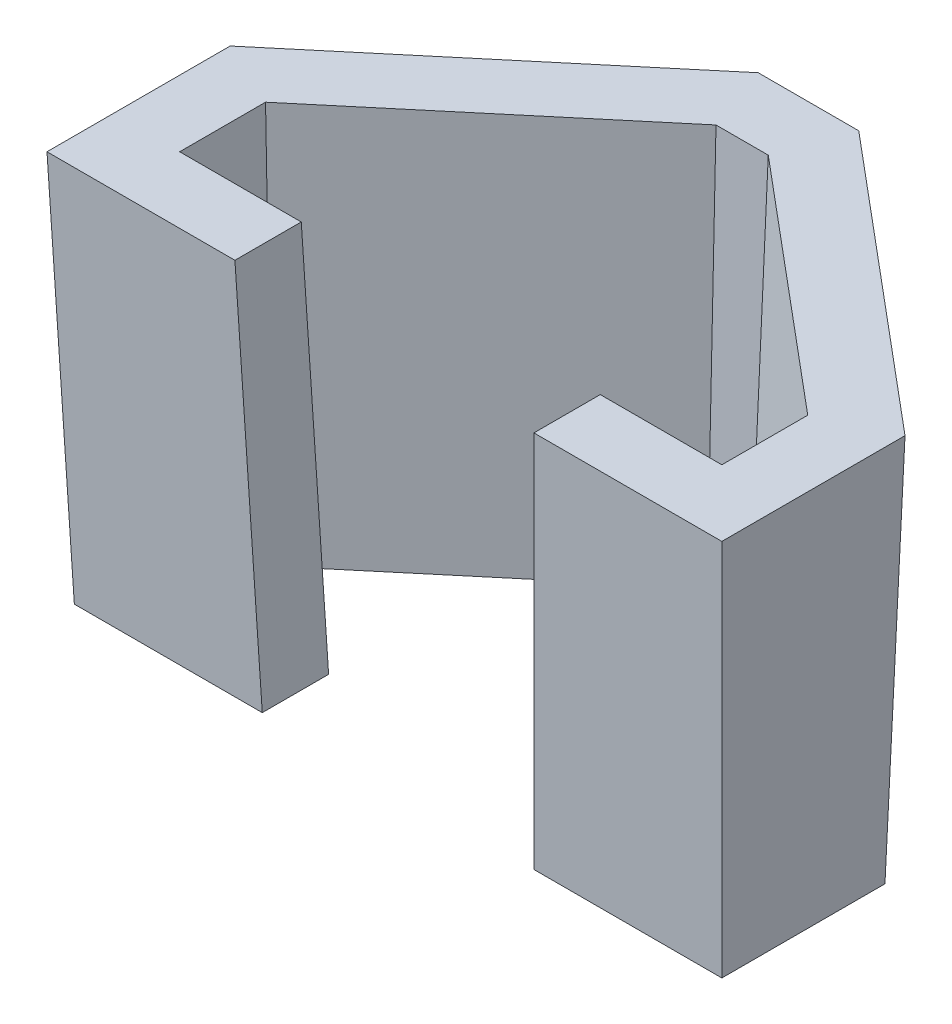
SolidWorks part; units mm, degrees
ref_plane "Alzado" through (0, 0, 0) normal (0, 0, 1) x (1, 0, 0)
ref_plane "Planta" through (0, 0, 0) normal (0, 1, 0) x (1, 0, 0)
ref_plane "Vista lateral" through (0, 0, 0) normal (1, 0, 0) x (0, 0, -1)
sketch "Croquis1" plane through (0, 0, 0) normal (0, 1, 0) x (1, 0, 0)
  line L0 (0, 0) -> (98.55, 0)
  line L1 (98.55, 0) -> (98.55, 12.6)
  line L2 (98.55, 12.6) -> (53.325, 50.5373)
  line L3 (53.325, 50.5373) -> (45.225, 50.5373)
  line L4 (45.225, 50.5373) -> (0, 12.6)
  line L5 (0, 12.6) -> (0, 0)
  point P7 (49.275, 50.5373)
  point P8 (49.275, 0)
  dimension "D1" = 98.55
  dimension "D2" = 8.1
  dimension "D3" = 59.03
  dimension "D4" = 59.03
  dimension "D5" = 12.6
extrude "Saliente-Extruir1" add sketch "Croquis1" along normal blind 8 draft 2 draft outward yes
sketch "Croquis10" plane through (0, 0, 0) normal (0, -1, 0) x (1, 0, 0)
  line L12 (-12.7, 12.7) -> (-12.7, -18.5232)
  line L13 (-12.7, -18.5232) -> (40.6036, -63.2373)
  line L14 (40.6036, -63.2373) -> (57.9464, -63.2373)
  line L15 (57.9464, -63.2373) -> (111.25, -18.5232)
  line L16 (111.25, -18.5232) -> (111.25, 12.7)
  line L17 (111.25, 12.7) -> (-12.7, 12.7)
  line L18 (-12.7, 12.7) -> (-12.7, -18.5232)
  line L19 (-12.7, -18.5232) -> (40.6036, -63.2373)
  line L20 (40.6036, -63.2373) -> (57.9464, -63.2373)
  line L21 (57.9464, -63.2373) -> (111.25, -18.5232)
  line L22 (111.25, -18.5232) -> (111.25, 12.7)
  line L23 (111.25, 12.7) -> (-12.7, 12.7)
  dimension "D1" = 12.7
extrude "Saliente-Extruir3" add sketch "Croquis10" against normal blind 75 draft 2 draft outward yes
sketch "Croquis11" plane through (0, 0, 0) normal (0, -1, 0) x (1, 0, 0)
  line L12 (98.55, 0) -> (0, 0)
  line L13 (98.55, -12.6) -> (98.55, 0)
  line L14 (53.325, -50.5373) -> (98.55, -12.6)
  line L15 (45.225, -50.5373) -> (53.325, -50.5373)
  line L16 (0, -12.6) -> (45.225, -50.5373)
  line L17 (0, 0) -> (0, -12.6)
  line L18 (98.55, 0) -> (0, 0)
  line L19 (98.55, -12.6) -> (98.55, 0)
  line L20 (53.325, -50.5373) -> (98.55, -12.6)
  line L21 (45.225, -50.5373) -> (53.325, -50.5373)
  line L22 (0, -12.6) -> (45.225, -50.5373)
  line L23 (0, 0) -> (0, -12.6)
  dimension "D1" = 0
extrude "Cortar-Extruir3" cut sketch "Croquis11" against normal through all draft 2 draft outward yes
sketch "Croquis13" plane through (0, 0, 0) normal (0, -1, 0) x (1, 0, 0)
  line L1 (0, 0) -> (0, -29.1767)
  line L3 (-12.7, -18.5232) -> (40.6036, -63.2373) construction
  line L4 (98.55, 0) -> (98.55, -29.1767)
  line L5 (57.9464, -63.2373) -> (111.25, -18.5232) construction
  line L18 (25.464, -50.5373) -> (73.086, -50.5373)
  line L19 (45.225, -50.5373) -> (53.325, -50.5373) construction
  line L20 (98.55, -12.6) -> (98.55, 0) construction
  line L21 (0, 0) -> (0, -12.6) construction
  line L22 (0, 0) -> (-12.7, 12.7)
  line L23 (98.55, 0) -> (111.25, 12.7)
sketch "Croquis14" plane through (0, 0, 0) normal (0, -1, 0) x (1, 0, 0)
  line L0 (111.25, 12.7) -> (-12.7, 12.7) construction
  line L1 (23.275, 0) -> (75.275, 0)
  line L2 (23.275, 0) -> (23.275, 12.7)
  line L3 (23.275, 12.7) -> (75.275, 12.7)
  line L4 (75.275, 0) -> (75.275, 12.7)
  line L5 (23.275, 0) -> (75.275, 12.7) construction
  line L6 (23.275, 12.7) -> (75.275, 0) construction
  line L7 (25.464, -50.5373) -> (73.086, -50.5373) construction
  line L8 (98.55, 0) -> (0, 0) construction
  point P0 (49.275, 6.35)
  point P7 (75.275, 6.35)
  point P11 (49.275, -50.5373)
  dimension "D1" = 52
extrude "Cortar-Extruir4" cut sketch "Croquis14" against normal through all draft 2 draft outward yes
